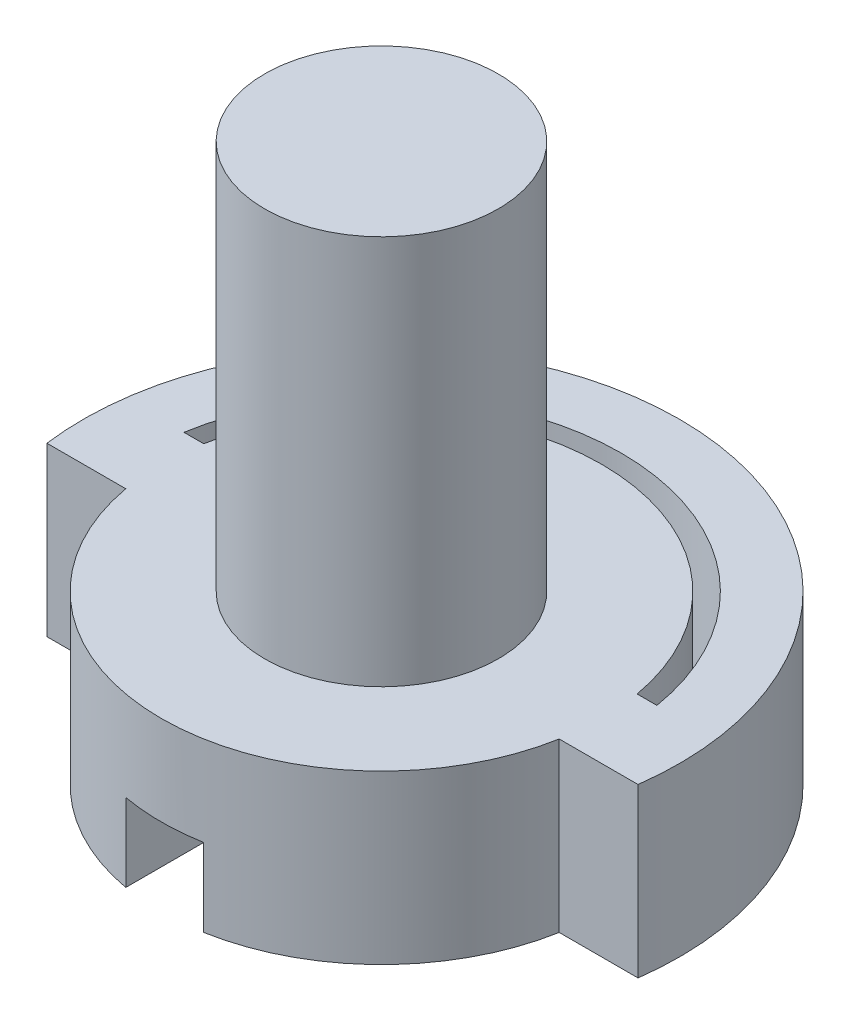
SolidWorks part; units mm, degrees
ref_plane "Front Plane" through (0, 0, 0) normal (0, 0, 1) x (1, 0, 0)
ref_plane "Top Plane" through (0, 0, 0) normal (0, 1, 0) x (1, 0, 0)
ref_plane "Right Plane" through (0, 0, 0) normal (1, 0, 0) x (0, 0, -1)
sketch "Sketch1" plane through (0, 0, 0) normal (0, 1, 0) x (1, 0, 0)
  line L1 (-25.7001, 1) -> (25.7001, 1)
  line L2 (-25.7001, 1) -> (-25.7001, -1)
  line L3 (-25.7001, -1) -> (25.7001, -1)
  line L4 (25.7001, 1) -> (25.7001, -1)
  line L5 (-25.7001, 1) -> (25.7001, -1) construction
  line L6 (-25.7001, -1) -> (25.7001, 1) construction
  circle A0 centre (0, 0) radius 5.65
  circle A1 centre (0, 0) radius 6.15
  circle A2 centre (0, 0) radius 7.65
  dimension "D1" = 1.5
  dimension "D3" = 0.5
  dimension "D4" = 15.3
  dimension "D2" = 2
extrude "Boss-Extrude1" add sketch "Sketch1" along normal blind 4.3 contours L3 A0 | L3 A0 L1 | L1 A0 | L1 A1 L3 A0 | L1 A2 L3 A1 | L1 A2 A1 | L3 A2 L1 A1 | L3 A1 L1 A0
sketch "Sketch2" plane through (0, 4.3, 0) normal (0, 1, 0) x (1, 0, 0)
  circle A0 centre (0, 0) radius 3
  dimension "D1" = 6
extrude "Boss-Extrude2" add sketch "Sketch2" along normal blind 10
sketch "Sketch3" plane through (0, 0, 0) normal (0, -1, 0) x (1, 0, 0)
  line L1 (-1, -5.9355) -> (1, -5.9355)
  line L2 (-1, -5.9355) -> (-1, 5.9355)
  line L3 (-1, 5.9355) -> (1, 5.9355)
  line L4 (1, -5.9355) -> (1, 5.9355)
  line L5 (-1, -5.9355) -> (1, 5.9355) construction
  line L6 (-1, 5.9355) -> (1, -5.9355) construction
  point P0 (0, 0)
  dimension "D1" = 2
extrude "Cut-Extrude1" cut sketch "Sketch3" against normal blind 2
